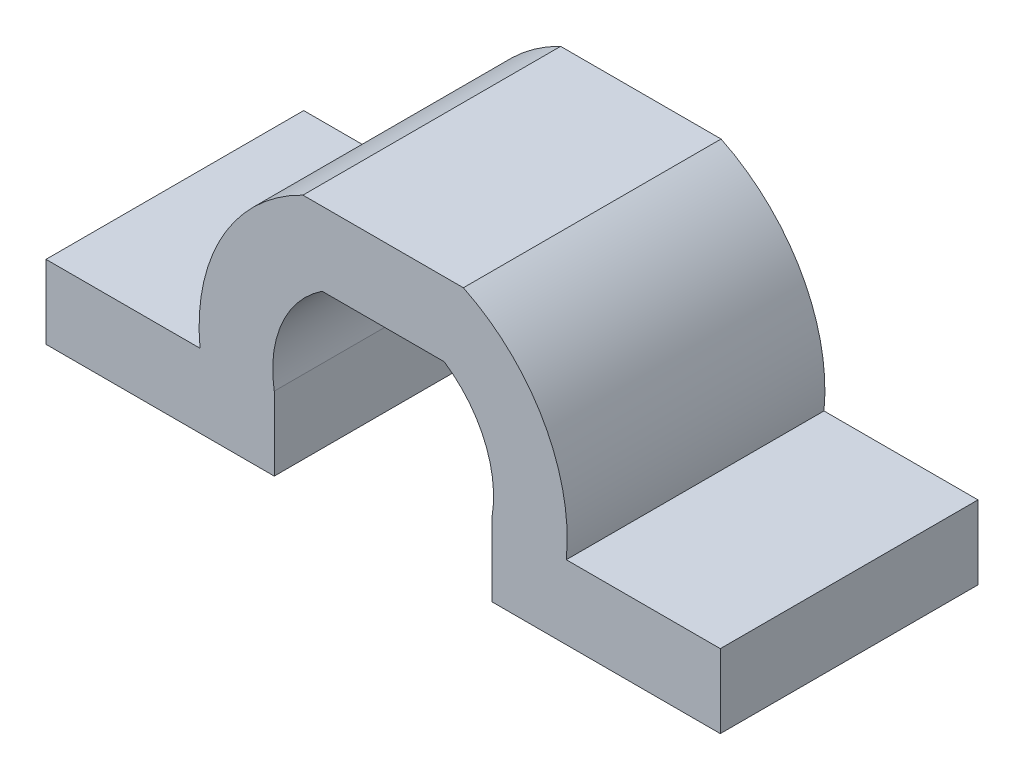
SolidWorks part; units mm, degrees
ref_plane "Alzado" through (0, 0, 0) normal (0, 0, 1) x (1, 0, 0)
ref_plane "Planta" through (0, 0, 0) normal (0, 1, 0) x (1, 0, 0)
ref_plane "Vista lateral" through (0, 0, 0) normal (1, 0, 0) x (0, 0, -1)
sketch "Croquis1" plane through (0, 0, 0) normal (0, 0, 1) x (1, 0, 0)
  line L1 (-3.3166, 5) -> (3.3166, 5)
  line L8 (0, 0) -> (0, 5) construction
  line L13 (-6, 0) -> (6, 0) construction
  line L14 (-3.3166, -5) -> (3.3166, -5) construction
  line L16 (-4.3589, 9) -> (4.3589, 9)
  line L17 (-5.9161, -5) -> (-18.3166, -5)
  line L18 (-18.3166, -5) -> (-18.3166, -1)
  line L19 (-18.3166, -1) -> (-9.9499, -1)
  line L20 (5.9161, -5) -> (18.3166, -5)
  line L21 (18.3166, -5) -> (18.3166, -1)
  line L22 (18.3166, -1) -> (9.9499, -1)
  line L23 (-4.3589, -9) -> (4.3589, -9) construction
  line L24 (-5.9161, -1) -> (-5.9161, -5)
  line L25 (5.9161, -1) -> (5.9161, -5)
  arc A0 (-3.3166, 5) -> (-5.9161, -1) centre (0, 0) ccw
  arc A1 (5.9161, -1) -> (3.3166, 5) centre (0, 0) ccw
  arc A4 (-4.3589, 9) -> (-9.9499, -1) centre (0, 0) ccw
  arc A5 (9.9499, -1) -> (4.3589, 9) centre (0, 0) ccw
  arc A6 (-4.3589, 9) -> (-4.3589, -9) centre (0, 0) ccw construction
  arc A7 (4.3589, -9) -> (4.3589, 9) centre (0, 0) ccw construction
  arc A8 (-3.3166, 5) -> (-3.3166, -5) centre (0, 0) ccw construction
  arc A9 (3.3166, -5) -> (3.3166, 5) centre (0, 0) ccw construction
  point P23 (0, 0)
  point P24 (0, 0)
  point P27 (0, 0)
  dimension "D1" = 12
  dimension "D2" = 5
  dimension "D3" = 4
  dimension "D4" = 15
  dimension "D5" = 4
  dimension "D6" = 2.5995
extrude "Saliente-Extruir2" add sketch "Croquis1" along normal blind 14 contours L22 A5 L16 A4 L19 L18 L17 A0 L1 A1 L20 L21
